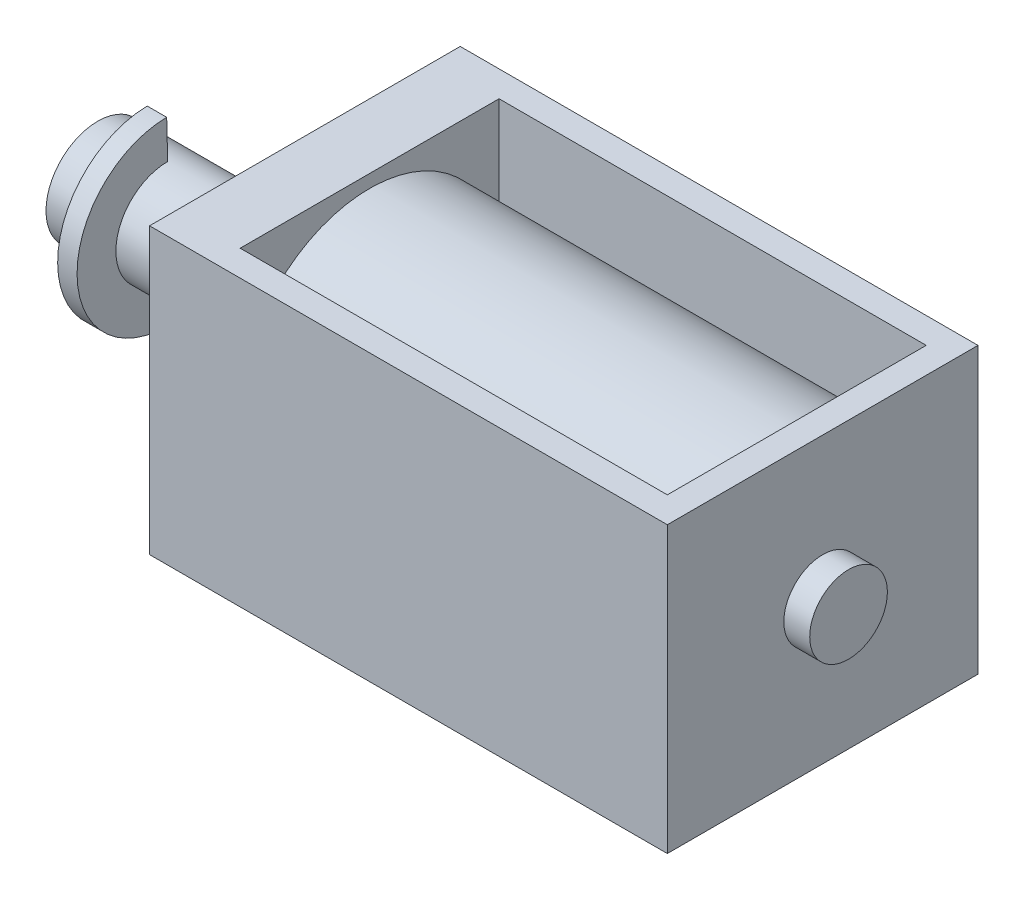
SolidWorks part; units mm, degrees
ref_plane "Front Plane" through (0, 0, 0) normal (0, 0, 1) x (1, 0, 0)
ref_plane "Top Plane" through (0, 0, 0) normal (0, 1, 0) x (1, 0, 0)
ref_plane "Right Plane" through (0, 0, 0) normal (1, 0, 0) x (0, 0, -1)
sketch "Sketch1" plane through (0, 0, 0) normal (0, 1, 0) x (1, 0, 0)
  line L1 (0, 0) -> (20, 0)
  line L2 (0, 0) -> (0, 12)
  line L3 (0, 12) -> (20, 12)
  line L4 (20, 0) -> (20, 12)
  dimension "D1" = 12
  dimension "D2" = 20
extrude "Boss-Extrude1" add sketch "Sketch1" along normal blind 11
sketch "Sketch3" plane through (0, 11, 0) normal (0, 1, 0) x (1, 0, 0)
  line L0 (0, 12) -> (20, 12) construction
  line L1 (2.5, 11) -> (19, 11)
  line L2 (2.5, 11) -> (2.5, 1)
  line L3 (2.5, 1) -> (19, 1)
  line L4 (19, 11) -> (19, 1)
  line L5 (0, 0) -> (20, 0) construction
  line L6 (20, 0) -> (20, 12) construction
  line L7 (0, 12) -> (0, 0) construction
  dimension "D1" = 1
  dimension "D2" = 1
  dimension "D3" = 1
  dimension "D4" = 2.5
extrude "Cut-Extrude1" cut sketch "Sketch3" against normal through all
sketch "Sketch4" plane through (2.5, 0, 0) normal (1, 0, 0) x (0, 0, -1)
  line L0 (6, 11) -> (6, 0) construction
  line L1 (0, 11) -> (12, 11) construction
  line L2 (0, 0) -> (12, 0) construction
  line L3 (11, 0) -> (11, 11) construction
  circle A0 centre (6, 5.5) radius 5
  point P8 (0, 0)
extrude "Boss-Extrude3" add sketch "Sketch4" along normal up to next separate body
sketch "Sketch5" plane through (0, 0, 0) normal (-1, 0, 0) x (0, 0, 1)
  line L0 (-12, 5.5) -> (0, 5.5) construction
  line L1 (-12, 11) -> (-12, 0) construction
  line L2 (0, 11) -> (0, 0) construction
  circle A0 centre (-6, 5.5) radius 2
  dimension "D1" = 4
extrude "Boss-Extrude4" add sketch "Sketch5" along normal blind 8
sketch "Sketch6" plane through (20, 0, 0) normal (1, 0, 0) x (0, 0, -1)
  line L0 (12, 5.5) -> (0, 5.5) construction
  line L1 (12, 11) -> (12, 0) construction
  line L2 (0, 11) -> (0, 0) construction
  circle A0 centre (6, 5.5) radius 1.5
  dimension "D1" = 3
extrude "Boss-Extrude5" add sketch "Sketch6" along normal blind 1
ref_plane "Plane2" through (-5.3, 0, 0) normal (-1, 0, 0) x (0, 0, 1)
sketch "Sketch7" plane through (-5.3, 0, 0) normal (-1, 0, 0) x (0, 0, 1)
  line L0 (-6, 7.5) -> (-5.9615, 8.9998)
  line L1 (-6, 3.5) -> (-6, 2)
  arc A0 (-6, 3.5) -> (-6, 7.5) centre (-6, 5.5) ccw
  circle A1 centre (-6, 5.5) radius 2 construction
  circle A2 centre (-6, 5.5) radius 2 construction
  arc A3 (-6, 2) -> (-5.9615, 8.9998) centre (-6, 5.5) ccw
  dimension "D1" = 3.5
extrude "Boss-Extrude6" add sketch "Sketch7" along normal blind 0.75
